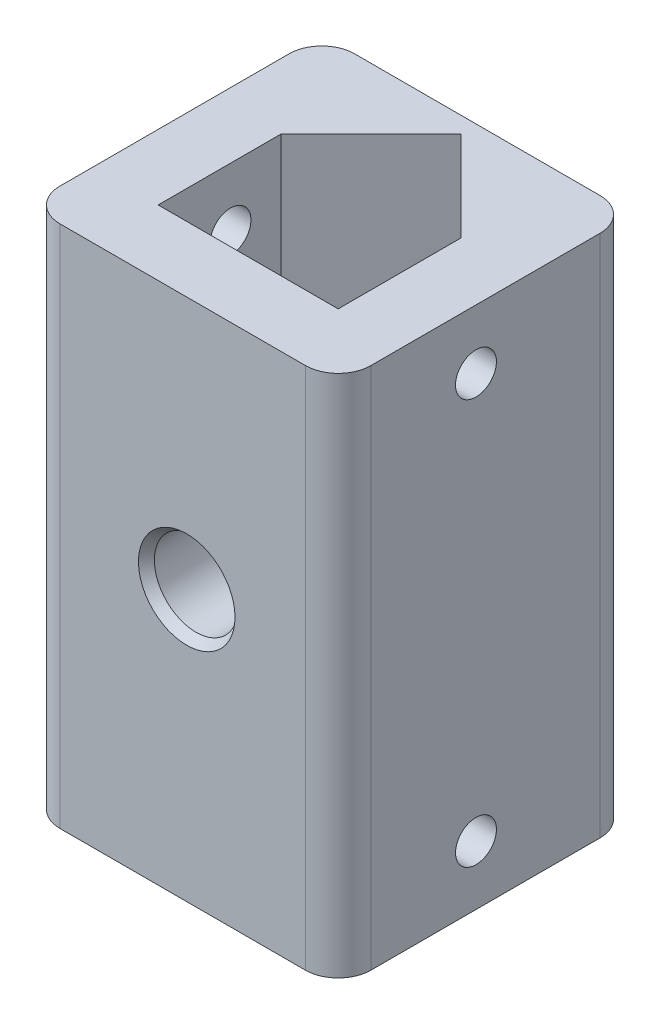
SolidWorks part; units mm, degrees
ref_plane "Front Plane" through (0, 0, 0) normal (0, 0, 1) x (1, 0, 0)
ref_plane "Top Plane" through (0, 0, 0) normal (0, 1, 0) x (1, 0, 0)
ref_plane "Right Plane" through (0, 0, 0) normal (1, 0, 0) x (0, 0, -1)
sketch "Sketch1" plane through (0, 0, 0) normal (0, 1, 0) x (1, 0, 0)
  line L0 (4, 4) -> (15, 4)
  line L1 (0, 0) -> (19, 0)
  line L2 (0, 0) -> (0, 18)
  line L3 (0, 18) -> (19, 18)
  line L4 (19, 0) -> (19, 18)
  line L5 (15, 4) -> (15, 11.5)
  line L6 (15, 11.5) -> (9.5, 17)
  line L7 (9.5, 17) -> (4, 11.5)
  line L8 (4, 11.5) -> (4, 4)
  circle A0 centre (9.5, 8.6887) radius 5 construction
  dimension "D10" = 10
  dimension "D1" = 19
  dimension "D2" = 18
  dimension "D3" = 90
  dimension "D4" = 9.5
  dimension "D5" = 11
  dimension "D6" = 4
  dimension "D7" = 7.5
  dimension "D8" = 7.5
  dimension "D9" = 4
extrude "Boss-Extrude1" add sketch "Sketch1" along normal blind 32
hole_wizard "Tap Drill for M3x0.5 Tap1" positions "Sketch2" profile "Sketch3" hole size "M3x0.5" standard "ANSI Metric" end condition through all
sketch "Sketch2" plane through (19, 0, 0) normal (1, 0, 0) x (0, 0, -1)
  point P0 (8.4192, 28.375)
  point P3 (8.4192, 3.625)
sketch "Sketch3" plane through (19, 28.375, -8.4192) normal (0, 1, 0) x (0, 0, -1)
  line L0 (0, 0) -> (0, 19)
  line L1 (0, 19) -> (1.25, 19)
  line L2 (1.25, 19) -> (1.25, 0)
  line L5 (1.25, 0) -> (0, 0)
  line L11 (0, -6.35) -> (0, 107.95) construction
  dimension "Thru Hole Dia." = 2.5
  dimension "Thru Hole Depth" = 19
fillet "Fillet1" radius 2 4 edges at (19, 16, -18) (19, 16, 0) (0, 16, -18) (0, 16, 0)
hole_wizard "M5 Clearance Hole1" positions "Sketch4" profile "Sketch5" hole size "M5" standard "ANSI Metric" end condition up to next
sketch "Sketch4" plane through (0, 0, 0) normal (0, 0, 1) x (1, 0, 0)
  point P0 (9.7444, 16.5211)
sketch "Sketch5" plane through (9.7444, 16.5211, 0) normal (1, 0, 0) x (0, -1, 0)
  line L0 (0, 0) -> (0, 4)
  line L1 (0, 4) -> (2.55, 4)
  line L2 (2.55, 4) -> (2.55, 0.5713)
  line L3 (2.55, 0.5713) -> (2.95, 0)
  line L5 (2.95, 0) -> (0, 0)
  line L6 (-2.55, 0.5713) -> (-2.95, 0) construction
  line L11 (0, -6.35) -> (0, 107.95) construction
  dimension "Thru Hole Dia." = 5.1
  dimension "Thru Hole Depth" = 4
  dimension "Near C'Sink Dia." = 5.9
  dimension "Near C'Sink Angle" = 70
